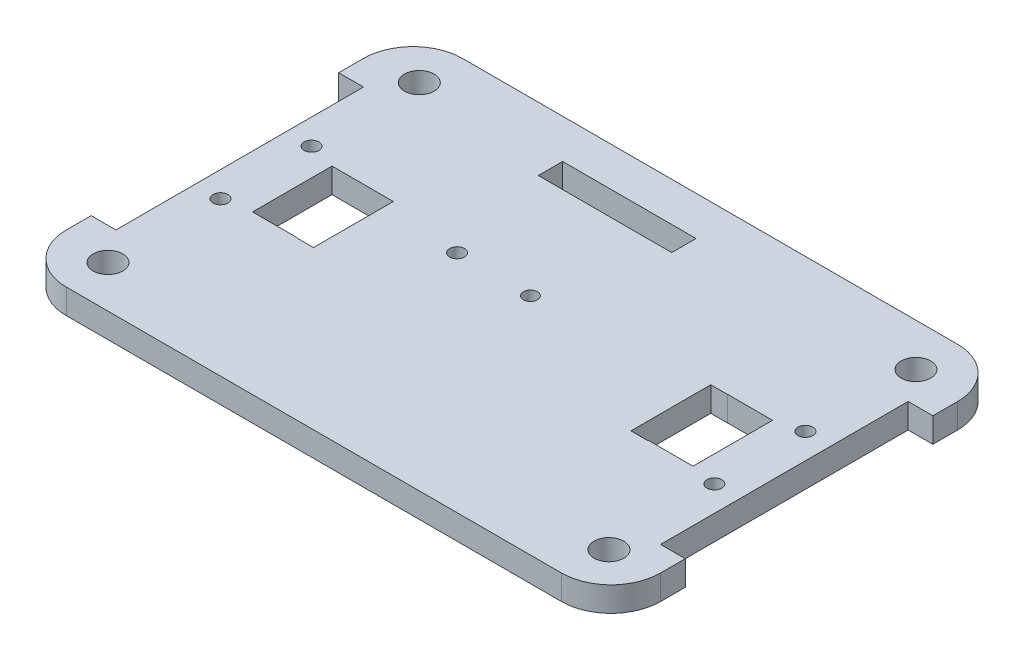
SolidWorks part; units mm, degrees
material "Acrylic (Medium-high impact)"
ref_plane "Front Plane" through (0, 0, 0) normal (0, 0, 1) x (1, 0, 0)
ref_plane "Top Plane" through (0, 0, 0) normal (0, 1, 0) x (1, 0, 0)
ref_plane "Right Plane" through (0, 0, 0) normal (1, 0, 0) x (0, 0, -1)
sketch "Sketch1" plane through (0, 0, 0) normal (0, 1, 0) x (1, 0, 0)
  line L0 (10, 0) -> (110, 0)
  line L3 (10, -80) -> (110, -80)
  line L4 (0, -10) -> (0, -15)
  line L5 (0, -70) -> (0, -65)
  line L6 (120, -10) -> (120, -15)
  line L7 (120, -70) -> (120, -65)
  line L8 (0, -15) -> (5, -15)
  line L9 (5, -15) -> (5, -65)
  line L10 (5, -65) -> (0, -65)
  line L11 (120, -15) -> (115, -15)
  line L12 (115, -15) -> (115, -65)
  line L13 (115, -65) -> (120, -65)
  arc A0 (120, -70) -> (110, -80) centre (110, -70) cw
  arc A1 (110, 0) -> (120, -10) centre (110, -10) cw
  arc A2 (0, -70) -> (10, -80) centre (10, -70) ccw
  arc A3 (10, 0) -> (0, -10) centre (10, -10) ccw
  point P15 (120, -80)
  point P18 (120, 0)
  point P21 (0, -80)
  point P24 (0, 0)
  dimension "D11" = 10
  dimension "D1" = 80
  dimension "D2" = 120
  dimension "D3" = 15
  dimension "D4" = 15
  dimension "D5" = 5
  dimension "D6" = 5
  dimension "D7" = 15
  dimension "D8" = 15
  dimension "D9" = 50
  dimension "D10" = 50
extrude "Boss-Extrude1" add sketch "Sketch1" along normal blind 5 contours L13 L7 A0 L3 A2 L5 L10 L9 L8 L4 A3 L0 A1 L6 L11 L12
sketch "Sketch2" plane through (0, 5, 0) normal (0, 1, 0) x (1, 0, 0)
  line L0 (0.189, -8.6122) -> (9.8714, -8.6088) construction
  line L1 (9.9933, -0.0789) -> (9.8714, -8.6088) construction
  line L2 (9.8868, -80.0249) -> (9.8429, -71.4949) construction
  line L3 (119.8458, -8.6842) -> (110.1658, -8.6599) construction
  line L4 (10.0313, -71.5863) -> (122.9526, -71.0617) construction
  line L5 (110.3621, -8.8959) -> (110.7556, -81.9472) construction
  circle A0 centre (9.8714, -8.5896) radius 3
  circle A1 centre (9.8798, -71.4816) radius 3.002
  circle A2 centre (110.7115, -71.1312) radius 2.9999
  circle A3 centre (110.1995, -8.6258) radius 2.9985
  dimension "D3" = 6
  dimension "D1" = 8.5299
  dimension "D2" = 9.6824
  dimension "D4" = 8.53
  dimension "D5" = 9.68
extrude "Cut-Extrude2" cut sketch "Sketch2" against normal blind 5 contours A2 | A1 | A0 | A3
sketch "Sketch6" plane through (0, 5, 0) normal (0, 1, 0) x (1, 0, 0)
  line L1 (60.0794, 0.2313) -> (60.1071, -80.0723) construction
  line L2 (95.5619, -47.9996) -> (104.5638, -48.02) construction
  line L3 (15.6122, -48.0195) -> (15.6122, -32.0209) construction
  line L4 (15.6623, -32.0193) -> (24.6629, -32.0193) construction
  line L5 (24.6629, -32.0193) -> (24.6301, -48.024) construction
  line L6 (24.6301, -48.024) -> (15.6283, -48.0506) construction
  line L7 (95.5182, -31.9949) -> (95.5619, -47.9996) construction
  line L8 (104.5187, -31.9887) -> (95.5182, -31.9949) construction
  line L9 (104.5799, -47.9889) -> (104.5688, -31.9902) construction
  line L11 (15.6499, -32.0049) -> (24.6615, -32.0049)
  line L12 (15.6499, -32.0049) -> (15.6499, -48.0508)
  line L13 (15.6499, -48.0508) -> (24.6615, -48.0508)
  line L14 (24.6615, -32.0049) -> (24.6615, -48.0508)
  line L15 (95.5443, -31.9858) -> (104.6006, -31.9858)
  line L16 (95.5443, -31.9858) -> (95.5443, -48.0407)
  line L17 (95.5443, -48.0407) -> (104.6006, -48.0407)
  line L18 (104.6006, -31.9858) -> (104.6006, -48.0407)
extrude "Cut-Extrude4" cut sketch "Sketch6" against normal blind 5
sketch "Sketch8" plane through (0, 5, 0) normal (0, 1, 0) x (1, 0, 0)
  line L0 (41.9521, -34.6532) -> (41.9561, -34.6532) construction
  line L7 (56.9429, -34.6181) -> (56.95, -34.6181) construction
  line L8 (59.7797, -34.6054) -> (59.7888, -34.6053) construction
  circle A0 centre (43.4487, -34.5359) radius 1.4972
  circle A1 centre (58.3696, -34.6609) radius 1.4203
extrude "Cut-Extrude6" cut sketch "Sketch8" against normal blind 5 contours A0 | A1
sketch "Sketch11" plane through (0, 5, 0) normal (0, 1, 0) x (1, 0, 0)
  line L0 (92.1545, -32.0125) -> (95.5253, -32.0125)
  line L1 (24.6615, -32.0049) -> (28.0323, -32.0049)
  line L2 (24.6615, -32.0049) -> (24.6615, -48.1276)
  line L3 (24.6615, -48.1276) -> (28.0323, -48.1276)
  line L4 (28.0323, -32.0049) -> (28.0323, -48.1276)
  line L5 (92.1545, -32.0125) -> (92.1545, -48.1353)
  line L6 (92.1545, -48.1353) -> (95.5253, -48.1353)
  line L7 (95.5253, -32.0125) -> (95.5253, -48.1353)
  circle A0 centre (10.1044, -30.5974) radius 1.4974
  circle A1 centre (10.1044, -48.9821) radius 1.4974
  circle A2 centre (109.853, -30.5974) radius 1.4974
  circle A3 centre (109.853, -48.9821) radius 1.4974
sketch "Sketch16" plane through (0, 5, 0) normal (0, 1, 0) x (1, 0, 0)
  line L1 (38.1322, -7.9089) -> (65.083, -7.9089)
  line L2 (38.1322, -7.9089) -> (38.1322, -12.8261)
  line L3 (38.1322, -12.8261) -> (65.083, -12.8261)
  line L4 (65.083, -7.9089) -> (65.083, -12.8261)
extrude "Cut-Extrude9" cut sketch "Sketch16" against normal blind 5 contours L2 L1 L4 L3
extrude "Cut-Extrude10" cut sketch "Sketch11" against normal blind 10
sketch "Sketch18" plane through (0, 5, 0) normal (0, 1, 0) x (1, 0, 0)
  line L0 (95.5253, -32.0125) -> (92.1545, -32.0125) construction
  line L1 (94.4558, -32.0125) -> (97.4252, -32.0125)
  line L2 (94.4558, -32.0125) -> (94.4558, -48.0407)
  line L3 (94.4558, -48.0407) -> (97.4252, -48.0407)
  line L4 (97.4252, -32.0125) -> (97.4252, -48.0407)
  line L5 (95.5443, -48.0407) -> (104.6006, -48.0407) construction
extrude "Cut-Extrude11" cut sketch "Sketch18" against normal blind 10
